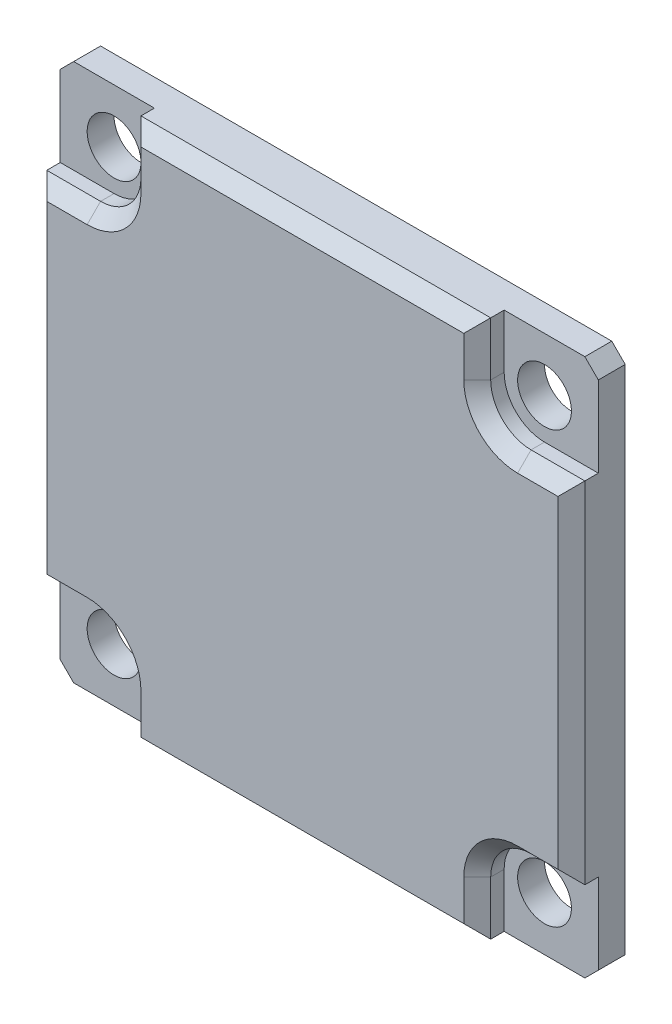
SolidWorks part; units mm, degrees
ref_plane "Alzado" through (0, 0, 0) normal (0, 0, 1) x (1, 0, 0)
ref_plane "Planta" through (0, 0, 0) normal (0, 1, 0) x (1, 0, 0)
ref_plane "Vista lateral" through (0, 0, 0) normal (1, 0, 0) x (0, 0, -1)
sketch "Croquis1" plane through (0, 0, 0) normal (0, 0, 1) x (1, 0, 0)
  line L0 (-20, 0) -> (20, 0) construction
  line L1 (20, 0) -> (20, 20) construction
  line L2 (20, 20) -> (-20, 20) construction
  line L3 (-20, 20) -> (-20, -20) construction
  line L4 (-20, -20) -> (20, -20) construction
  line L5 (20, -20) -> (20, 0) construction
  line L6 (-20, -20) -> (-16, -20) construction
  line L7 (-16, -20) -> (-16, -16) construction
  line L8 (0, -20) -> (0, 20) construction
  line L9 (-17, 0) -> (-14, 0) construction
  line L10 (-14, 0) -> (17, 0) construction
  line L11 (17, 0) -> (14, 0) construction
  line L13 (-20, -20) -> (20, -20)
  line L14 (-20, -20) -> (-20, 20)
  line L15 (-20, 20) -> (20, 20)
  line L16 (20, -20) -> (20, 20)
  circle A0 centre (-16, -16) radius 2
  circle A1 centre (16, -16) radius 2
  circle A2 centre (16, 16) radius 2
  circle A3 centre (-16, 16) radius 2
  circle A4 centre (0, 0) radius 17
extrude "Saliente-Extruir1" add sketch "Croquis1" along normal blind 3
sketch "Croquis2" plane through (0, 0, 3) normal (0, 0, 1) x (1, 0, 0)
  line L1 (-20, 20) -> (20, 20)
  line L2 (-20, 20) -> (-20, -20)
  line L3 (-20, -20) -> (20, -20)
  line L4 (20, 20) -> (20, -20)
extrude "Saliente-Extruir2" add sketch "Croquis2" along normal blind 1
sketch "Croquis3" plane through (0, 0, 4) normal (0, 0, 1) x (1, 0, 0)
  line L0 (-20, 20) -> (-16, 20) construction
  line L1 (20, 20) -> (-20, 20) construction
  line L2 (13, 16) -> (13, 20)
  line L3 (0, 0) -> (0, 50000) construction
  line L4 (0, 0) -> (50000, 0) construction
  line L5 (-13, 16) -> (-13, 20)
  line L6 (-16, 13) -> (-20, 13)
  line L7 (-20, 20) -> (-20, -20) construction
  line L8 (-20, 13) -> (-20, 20)
  line L9 (-20, 20) -> (-13, 20)
  line L10 (20, 20) -> (13, 20)
  line L11 (20, 13) -> (20, 20)
  line L12 (16, 13) -> (20, 13)
  line L13 (16, -13) -> (20, -13)
  line L14 (20, -13) -> (20, -20)
  line L15 (20, -20) -> (13, -20)
  line L16 (13, -16) -> (13, -20)
  line L17 (-13, -16) -> (-13, -20)
  line L18 (-20, -20) -> (-13, -20)
  line L19 (-20, -13) -> (-20, -20)
  line L20 (-16, -13) -> (-20, -13)
  arc A0 (-16, 13) -> (-13, 16) centre (-16, 16) ccw
  arc A1 (16, 13) -> (13, 16) centre (16, 16) cw
  arc A2 (16, -13) -> (13, -16) centre (16, -16) ccw
  arc A3 (-16, -13) -> (-13, -16) centre (-16, -16) cw
extrude "Cortar-Extruir1" cut sketch "Croquis3" against normal blind 2
chamfer "Chaflán1" distance 1 angle 45 20 edges at (-13.8787, -13.8787, 4) (-18, -13, 4) (-20, 0, 4) (-18, 13, 4) (-13.8787, 13.8787, 4) (-13, 18, 4) (0, 20, 4) (13, 18, 4) (13.8787, 13.8787, 4) (18, 13, 4) (20, 0, 4) (18, -13, 4) (13.8787, -13.8787, 4) (13, -18, 4) (0, -20, 4) (-13, -18, 4) (-20, -20, 1) (20, -20, 1) (20, 20, 1) (-20, 20, 1)
